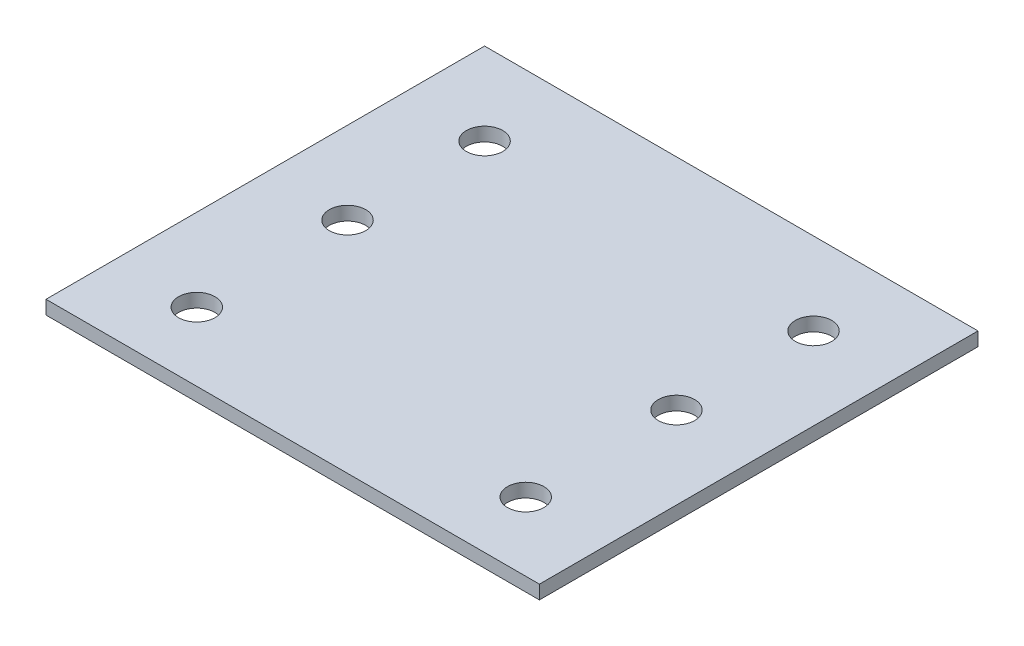
SolidWorks part; units mm, degrees
ref_plane "Front Plane" through (0, 0, 0) normal (0, 0, 1) x (1, 0, 0)
ref_plane "Top Plane" through (0, 0, 0) normal (0, 1, 0) x (1, 0, 0)
ref_plane "Right Plane" through (0, 0, 0) normal (1, 0, 0) x (0, 0, -1)
sketch "Sketch1" plane through (0, 0, 0) normal (0, 1, 0) x (1, 0, 0)
  line L1 (-57.15, 50.8) -> (57.15, 50.8)
  line L2 (-57.15, 50.8) -> (-57.15, -50.8)
  line L3 (-57.15, -50.8) -> (57.15, -50.8)
  line L4 (57.15, 50.8) -> (57.15, -50.8)
  line L5 (-57.15, 50.8) -> (57.15, -50.8) construction
  line L6 (-57.15, -50.8) -> (57.15, 50.8) construction
  point P0 (0, 0)
  dimension "D1" = 114.3
  dimension "D2" = 101.6
extrude "Boss-Extrude1" add sketch "Sketch1" along normal blind 3.175
sketch "Sketch7" plane through (0, 3.175, 0) normal (0, 1, 0) x (1, 0, 0)
  line L0 (-38.1, 50.8) -> (-38.1, -50.8) construction
  line L1 (-57.15, -50.8) -> (57.15, -50.8) construction
  line L2 (57.15, 50.8) -> (-57.15, 50.8) construction
  line L3 (-57.15, 50.8) -> (-57.15, -50.8) construction
  point P4 (-38.1, -31.75)
  point P9 (-38.1, 31.75)
  point P10 (-38.1, 0)
  point P11 (-38.1, -34.925)
  dimension "D1" = 19.05
  dimension "D2" = 19.05
  dimension "D3" = 19.05
  dimension "D4" = 34.925
hole_wizard "5/16 Clearance Hole1" [suppressed] positions "Sketch8" profile "Sketch9" hole size "5/16" standard "ANSI Inch"
sketch "Sketch8" plane through (0, 3.175, 0) normal (0, 1, 0) x (1, 0, 0)
  point P0 (-38.1, 31.75)
  point P3 (-38.1, -31.75)
sketch "Sketch9" plane through (-38.1, 3.175, -31.75) normal (1, 0, 0) x (0, 0, 1)
  line L0 (0, 0) -> (0, 3.175)
  line L1 (0, 3.175) -> (4.2164, 3.175)
  line L2 (4.2164, 3.175) -> (4.2164, 0)
  line L5 (4.2164, 0) -> (0, 0)
  line L11 (0, -6.35) -> (0, 107.95) construction
  dimension "Thru Hole Dia." = 8.4328
  dimension "Thru Hole Depth" = 3.175
mirror "Mirror1" [suppressed] about plane through (0, 0, 0) normal (1, 0, 0)
hole_wizard "5/16 Clearance Hole2" positions "Sketch10" profile "Sketch11" hole size "5/16" standard "ANSI Inch" end condition through all
sketch "Sketch10" plane through (0, 3.175, 0) normal (0, 1, 0) x (1, 0, 0)
  point P0 (-38.1, 31.75)
  point P3 (-38.1, 0)
  point P6 (-38.1, -34.925)
sketch "Sketch11" plane through (-38.1, 3.175, -31.75) normal (1, 0, 0) x (0, 0, 1)
  line L0 (0, 0) -> (0, 3.175)
  line L1 (0, 3.175) -> (4.2164, 3.175)
  line L2 (4.2164, 3.175) -> (4.2164, 0)
  line L5 (4.2164, 0) -> (0, 0)
  line L11 (0, -6.35) -> (0, 107.95) construction
  dimension "Thru Hole Dia." = 8.4328
  dimension "Thru Hole Depth" = 3.175
mirror "Mirror2" about plane through (0, 0, 0) normal (1, 0, 0) of "5/16 Clearance Hole2"
equation "\"from_end\"= 0.75in"
equation "\"D2@Sketch7\"=\"from_end\""
